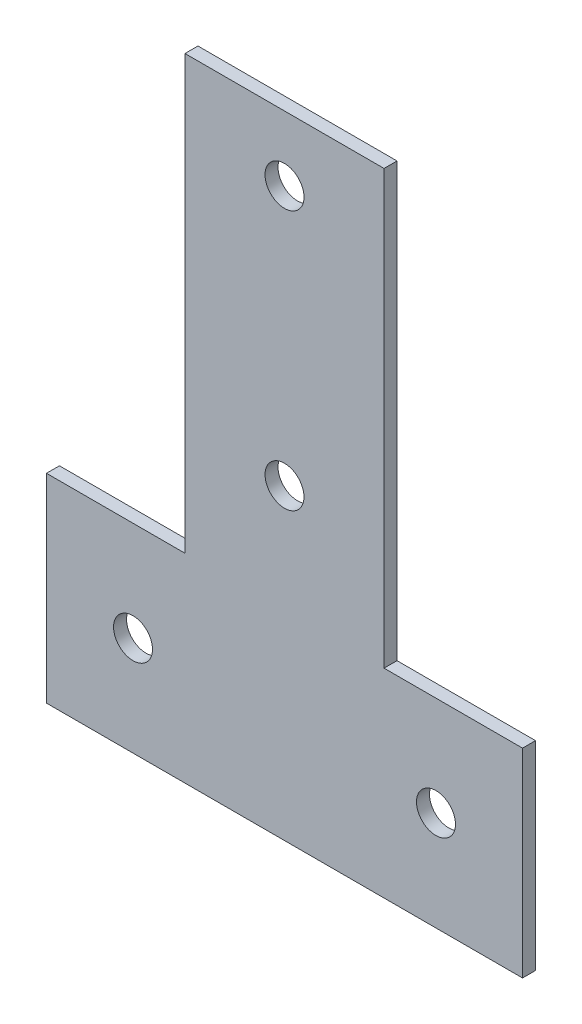
SolidWorks part; units mm, degrees
ref_plane "Спереди" through (0, 0, 0) normal (0, 0, 1) x (1, 0, 0)
ref_plane "Сверху" through (0, 0, 0) normal (0, 1, 0) x (1, 0, 0)
ref_plane "Справа" through (0, 0, 0) normal (1, 0, 0) x (0, 0, -1)
sketch "Эскиз1" plane through (0, 0, 0) normal (0, 0, 1) x (1, 0, 0)
  line L0 (-55, 0) -> (55, 0)
  line L1 (-55, 0) -> (-55, 46)
  line L2 (-55, 46) -> (-23, 46)
  line L3 (-23, 46) -> (-23, 146)
  line L4 (-23, 146) -> (23, 146)
  line L5 (23, 146) -> (23, 46)
  line L6 (23, 46) -> (55, 46)
  line L7 (55, 46) -> (55, 0)
  line L8 (-35, 23) -> (35, 23) construction
  circle A0 centre (0, 131) radius 4.5
  circle A1 centre (0, 71) radius 4.5
  circle A2 centre (-35, 23) radius 4.5
  circle A3 centre (35, 23) radius 4.5
  point P4 (0, 0)
  point P18 (0, 23)
  point P19 (55, 23)
  dimension "D5" = 15
  dimension "D6" = 60
  dimension "D7" = 9
  dimension "D1" = 110
  dimension "D2" = 146
  dimension "D3" = 46
  dimension "D4" = 70
extrude "Бобышка-Вытянуть1" add sketch "Эскиз1" along normal blind 3
